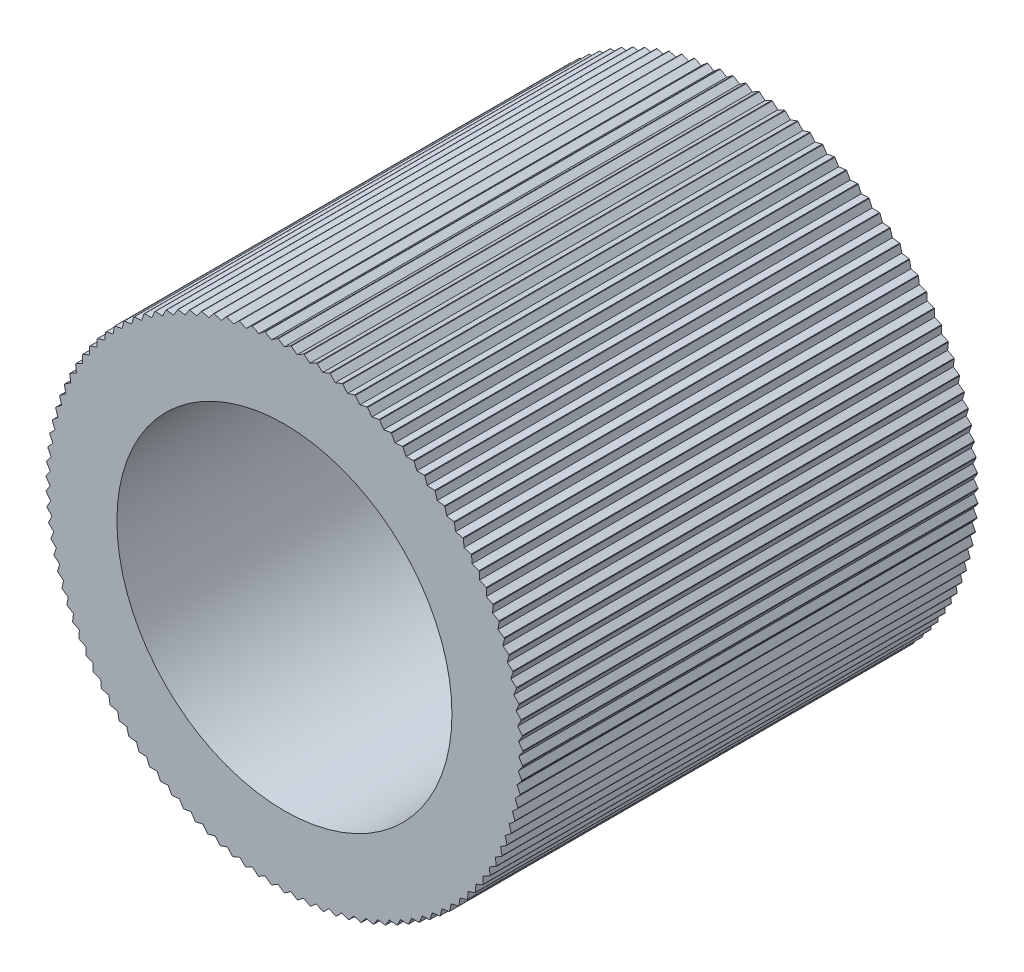
SolidWorks part; units mm, degrees
ref_plane "Alzado" through (0, 0, 0) normal (0, 0, 1) x (1, 0, 0)
ref_plane "Planta" through (0, 0, 0) normal (0, 1, 0) x (1, 0, 0)
ref_plane "Vista lateral" through (0, 0, 0) normal (1, 0, 0) x (0, 0, -1)
sketch "Croquis1" plane through (0, 0, 0) normal (0, 0, 1) x (1, 0, 0)
  circle A0 centre (0, 0) radius 3.85
  dimension "D1" = 7.7
extrude "Saliente-Extruir1" add sketch "Croquis1" along normal blind 7.35
hole_wizard "Perforador para roscar para macho de roscar para 1/4-281" positions "Croquis3" profile "Croquis2" hole size "1/4-28" standard "Ansi Inch" end condition up to next
sketch "Croquis3" plane through (0, 0, 7.35) normal (0, 0, 1) x (1, 0, 0)
  point P0 (0, 0)
sketch "Croquis2" plane through (0, 0, 7.35) normal (1, 0, 0) x (0, -1, 0)
  line L0 (0, 0) -> (0, 7.35)
  line L1 (0, 7.35) -> (2.7051, 7.35)
  line L2 (2.7051, 7.35) -> (2.7051, 0)
  line L5 (2.7051, 0) -> (0, 0)
  line L11 (0, -6.35) -> (0, 107.95) construction
  dimension "Diámetro de taladro hasta el siguiente" = 5.4102
  dimension "Profundidad de taladro hasta el siguiente" = 7.35
sketch "Croquis4" plane through (0, 0, 7.35) normal (0, 0, 1) x (1, 0, 0)
  line L0 (0, 3.85) -> (0, -3.85) construction
  line L5 (-0.1, 3.8487) -> (0, 3.7835)
  line L6 (0, 3.7835) -> (0.1, 3.8487)
  circle A0 centre (0, 0) radius 3.85 construction
  arc A1 (0.1, 3.8487) -> (-0.1, 3.8487) centre (0, 0) ccw
extrude "Cortar-Extruir1" cut sketch "Croquis4" against normal blind 7.35
pattern_circular "MatrizC1" count 115 over 360 about axis through (0, 0, 0) along (0, 0, 1) of "Cortar-Extruir1"
